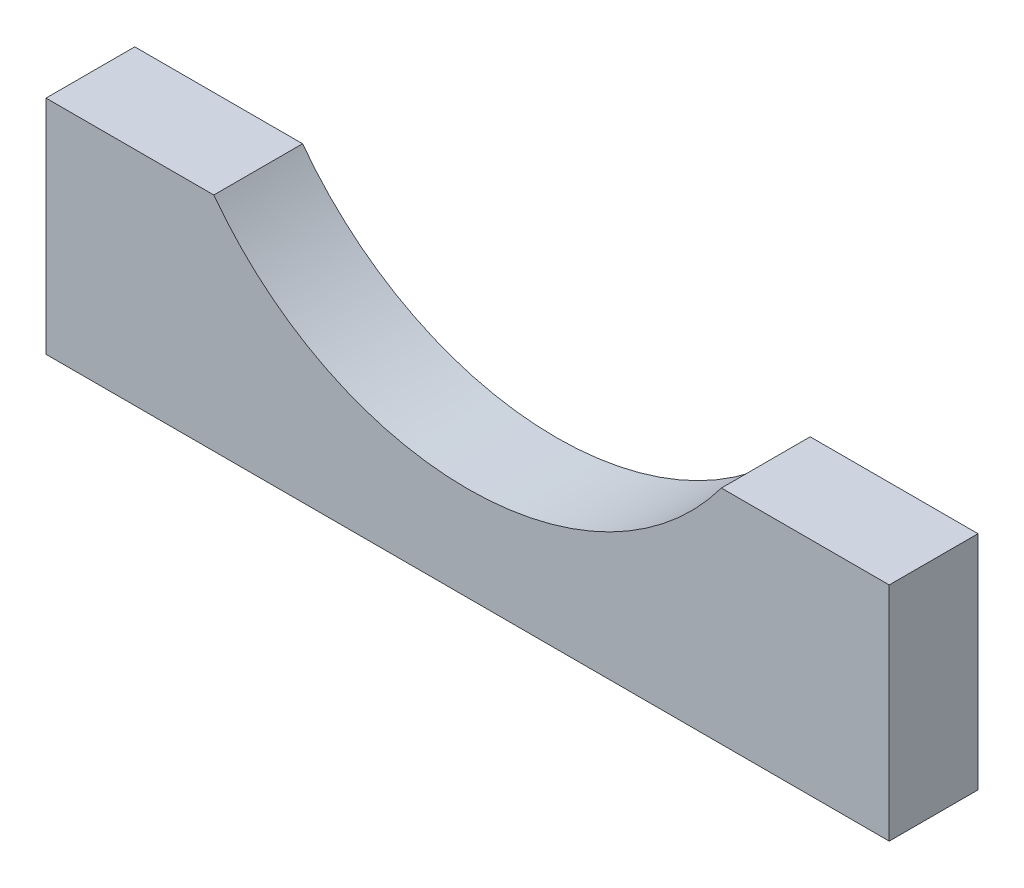
SolidWorks part; units mm, degrees
ref_plane "Front Plane" through (0, 0, 0) normal (0, 0, 1) x (1, 0, 0)
ref_plane "Top Plane" through (0, 0, 0) normal (0, 1, 0) x (1, 0, 0)
ref_plane "Right Plane" through (0, 0, 0) normal (1, 0, 0) x (0, 0, -1)
sketch "Sketch2" plane through (0, 0, 0) normal (0, 0, 1) x (1, 0, 0)
  line L5 (0, 0) -> (38, 0)
  line L6 (38, 0) -> (38, 10)
  line L7 (38, 10) -> (0, 10)
  line L12 (0, 10) -> (0, 0)
  dimension "D1" = 38
  dimension "D2" = 10
extrude "Boss-Extrude2" add sketch "Sketch2" along normal blind 4 contours L12 L5 L6 L7
sketch "Sketch3" plane through (0, 0, 4) normal (0, 0, 1) x (1, 0, 0)
  line L0 (0, 0) -> (38, 0) construction
  line L2 (38, 0) -> (38, 10) construction
  circle A0 centre (19, 18.5) radius 14.25
  point P6 (38, 5.4225)
  dimension "D1" = 28.5
  dimension "D3" = 19
  dimension "D2" = 18.5
extrude "Cut-Extrude1" cut sketch "Sketch3" against normal blind 10
